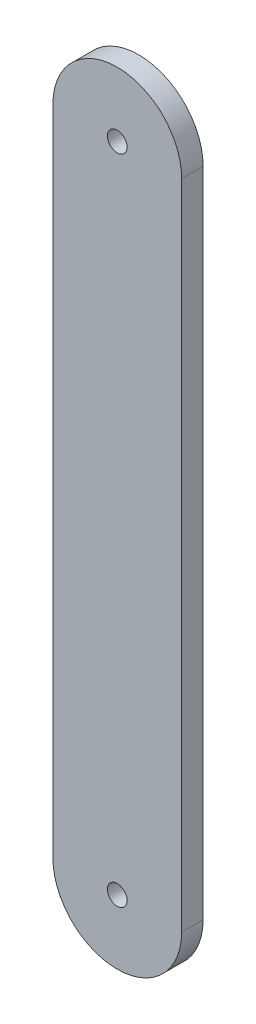
SolidWorks part; units mm, degrees
ref_plane "Front Plane" through (0, 0, 0) normal (0, 0, 1) x (1, 0, 0)
ref_plane "Top Plane" through (0, 0, 0) normal (0, 1, 0) x (1, 0, 0)
ref_plane "Right Plane" through (0, 0, 0) normal (1, 0, 0) x (0, 0, -1)
sketch "Sketch1" plane through (0, 0, 0) normal (0, 0, 1) x (1, 0, 0)
  line L0 (-19.353, 0) -> (-19.353, 96.52)
  line L2 (-0.303, 96.52) -> (-0.303, 0)
  arc A0 (-19.353, 96.52) -> (-0.303, 96.52) centre (-9.828, 96.52) cw
  arc A1 (-19.353, 0) -> (-0.303, 0) centre (-9.828, 0) ccw
  circle A2 centre (-9.828, 0) radius 1.4605
  circle A3 centre (-9.828, 96.52) radius 1.4605
  dimension "D2" = 2.921
  dimension "D3" = 2.921
  dimension "D1" = 96.52
  dimension "D4" = 19.05
extrude "Boss-Extrude1" add sketch "Sketch1" along normal blind 3.175
